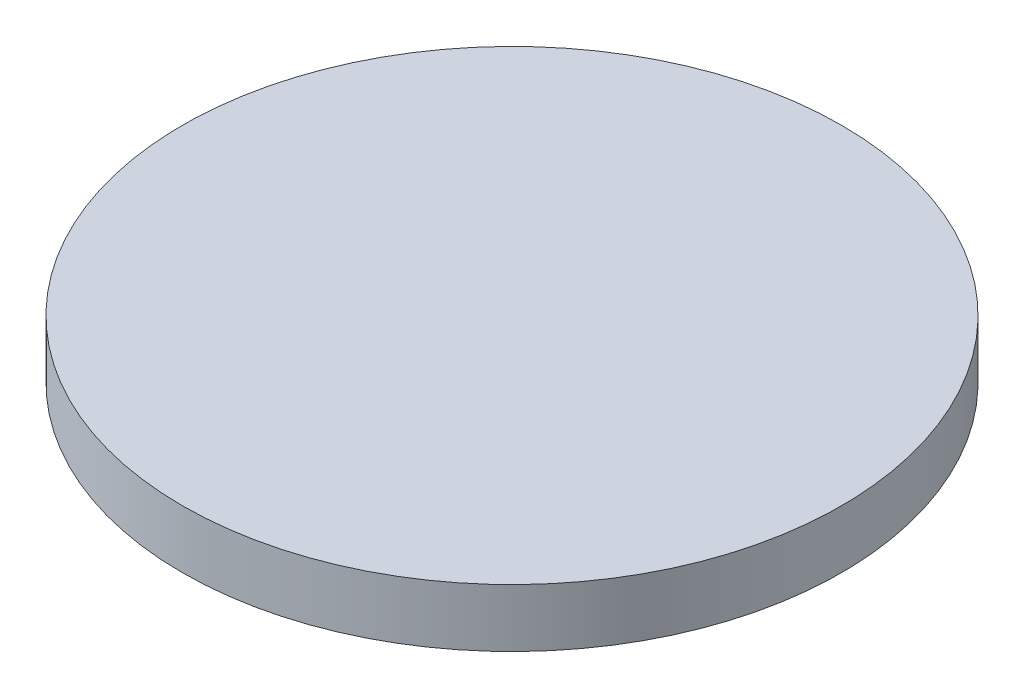
SolidWorks part; units mm, degrees
ref_plane "前视基准面" through (0, 0, 0) normal (0, 0, 1) x (1, 0, 0)
ref_plane "上视基准面" through (0, 0, 0) normal (0, 1, 0) x (1, 0, 0)
ref_plane "右视基准面" through (0, 0, 0) normal (1, 0, 0) x (0, 0, -1)
sketch "草图1" plane through (0, 0, 0) normal (0, 1, 0) x (1, 0, 0)
  circle A0 centre (0, 0) radius 6.25
  dimension "D1" = 12.5
extrude "凸台-拉伸1" add sketch "草图1" along normal blind 1.1
